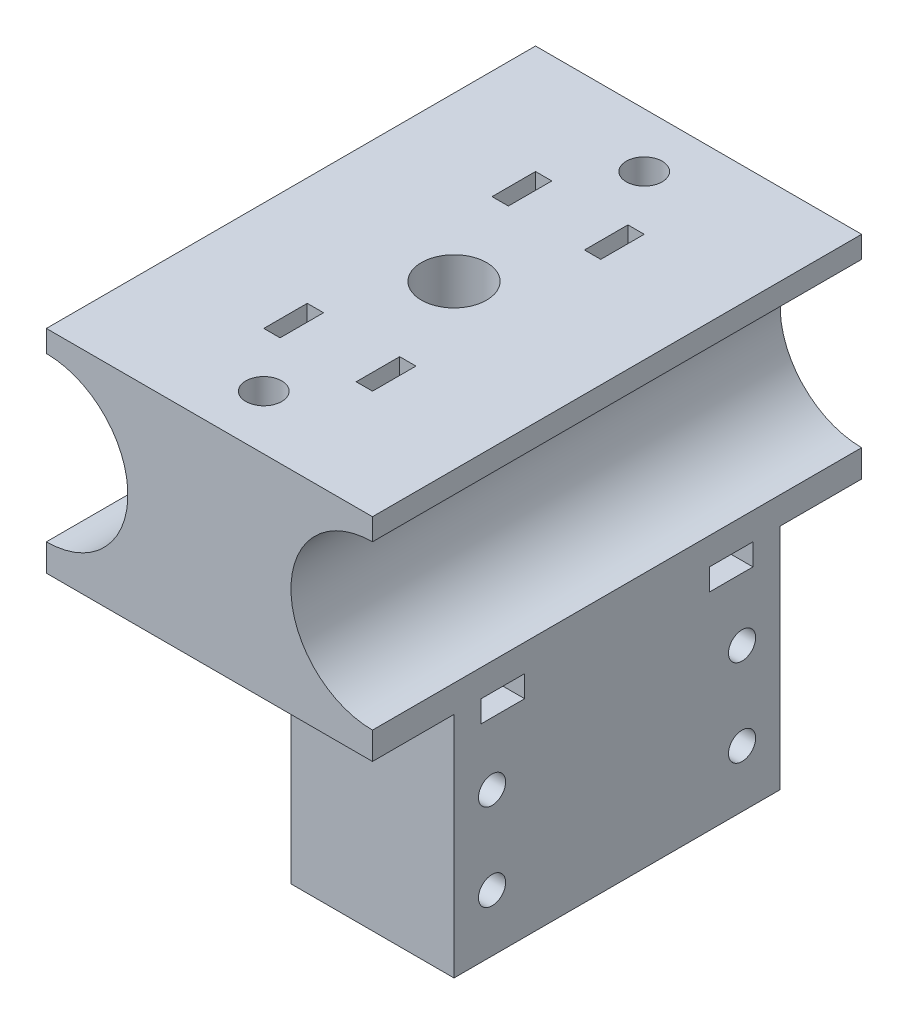
SolidWorks part; units mm, degrees
material "ABS"
ref_plane "Front Plane" through (0, 0, 0) normal (0, 0, 1) x (1, 0, 0)
ref_plane "Top Plane" through (0, 0, 0) normal (0, 1, 0) x (1, 0, 0)
ref_plane "Right Plane" through (0, 0, 0) normal (1, 0, 0) x (0, 0, -1)
sketch "Sketch1" plane through (0, 0, 0) normal (0, 0, 1) x (1, 0, 0)
  line L0 (15, 0) -> (-15, 0) construction
  line L5 (-15, 7.5) -> (-15, 9.5)
  line L6 (-15, 9.5) -> (15, 9.5)
  line L7 (15, 7.5) -> (15, 9.5)
  line L9 (-15, -7.5) -> (-15, -10)
  line L10 (-15, -10) -> (15, -10)
  line L11 (15, -7.5) -> (15, -10)
  arc A0 (15, 7.5) -> (15, -7.5) centre (15, 0) ccw
  arc A1 (-15, -7.5) -> (-15, 7.5) centre (-15, 0) ccw
  point P8 (0, 0)
  dimension "D2" = 15
  dimension "D1" = 30
  dimension "D3" = 2.5
  dimension "D4" = 2
extrude "Boss-Extrude1" add sketch "Sketch1" along normal mid plane 45
sketch "Sketch3" plane through (0, 0, 0) normal (0, 0, 1) x (1, 0, 0)
  line L0 (0, 9.5) -> (0, -10)
  line L1 (0, -10) -> (8, -10)
  line L2 (8, -10) -> (8, -3.25)
  line L3 (8, -3.25) -> (6, -3.25)
  line L4 (6, -3.25) -> (6, 2.75)
  line L5 (6, 2.75) -> (8, 2.75)
  line L6 (8, 2.75) -> (8, 9.5)
  line L7 (8, 9.5) -> (0, 9.5)
  line L8 (15, 9.5) -> (-15, 9.5) construction
  line L9 (-15, -10) -> (15, -10) construction
  dimension "D1" = 6
  dimension "D2" = 8
  dimension "D3" = 6
revolve "Cut-Revolve1" [suppressed] cut sketch "Sketch3" angle 360 about L0
hole_wizard "M4x0.7 Tapped Hole2" positions "Sketch5" profile "Sketch4" tap size "M4x0.7" standard "ANSI Metric" end condition through all
sketch "Sketch5" plane through (0, -10, 0) normal (0, -1, 0) x (-1, 0, 0)
  line L0 (0, 17.5) -> (0, -17.5) construction
  line L2 (15, -22.5) -> (-15, -22.5) construction
  point P0 (0, -17.5)
  point P2 (0, 17.5)
  dimension "D1" = 5
sketch "Sketch4" plane through (0, -10, 17.5) normal (1, 0, 0) x (0, 0, -1)
  line L0 (0, 0) -> (0, 19.5)
  line L1 (0, 19.5) -> (1.65, 19.5)
  line L2 (1.65, 19.5) -> (1.65, 0)
  line L5 (1.65, 0) -> (0, 0)
  line L11 (0, -6.35) -> (0, 107.95) construction
  dimension "Thru Tap Drill Dia." = 3.3
  dimension "Thru Tap Drill Depth" = 19.5
cosmetic thread "Hole Thread1" parameters "D2"=4
cosmetic thread "Hole Thread2" parameters "D2"=4
sketch "Sketch12" plane through (0, 0, 0) normal (0, 0, 1) x (1, 0, 0)
  line L0 (0, 0) -> (0, -31) construction
  line L1 (8, -31) -> (8, -24.5)
  line L2 (8, -24.5) -> (6, -24.5)
  line L3 (6, -24.5) -> (6, -19)
  line L4 (6, -19) -> (8, -19)
  line L5 (8, -19) -> (8, -10)
  line L9 (8, -10) -> (15, -10)
  line L10 (15, -10) -> (15, -31)
  line L11 (15, -31) -> (8, -31)
  dimension "D1" = 5.5
  dimension "D2" = 8
  dimension "D3" = 6.5
  dimension "D4" = 6
  dimension "D5" = 9
revolve "Revolve1" add sketch "Sketch12" angle 180 mid plane about L0
sketch "Sketch15" plane through (0, -31, 0) normal (0, -1, 0) x (1, 0, 0)
  line L7 (0, 15) -> (15, 15)
  line L8 (15, 22.5) -> (15, 0) construction
  line L9 (0, -8) -> (0, -15)
  line L10 (0, 15) -> (0, 8)
  line L13 (15, 15) -> (15, -15)
  line L14 (15, 0) -> (15, -22.5) construction
  line L15 (15, -15) -> (0, -15)
  arc A5 (0, -8) -> (0, 8) centre (0, 0) ccw
  arc A6 (0, -15) -> (0, 15) centre (0, 0) ccw
  arc A8 (0, -15) -> (0, 15) centre (0, 0) ccw
  arc M7 (0, -15) -> (0, 15) centre (0, 0) ccw
  dimension "D1" = 0
extrude "Boss-Extrude4" add sketch "Sketch15" against normal up to next contours L13 L7 M7 | L15 L13 M7
hole_wizard "M3x0.5 Tapped Hole1" positions "Sketch13" profile "Sketch14" tap size "M3x0.5" standard "ANSI Metric" end condition through all
sketch "Sketch13" plane through (0, 0, 0) normal (-1, 0, 0) x (0, 0, 1)
  line L0 (0, 0) -> (0, -31) construction
  line L3 (0, -21.75) -> (-11.5, -21.75) construction
  line L6 (-11.5, -17.75) -> (-11.5, -25.75) construction
  line L8 (-6, -19) -> (-6, -24.5) construction
  line L9 (-8, -31) -> (8, -31) construction
  point P0 (-11.5, -17.75)
  point P2 (-11.5, -25.75)
  point P4 (11.5, -25.75)
  point P6 (11.5, -17.75)
  point P27 (-6, -21.75)
  dimension "D1" = 8
  dimension "D2" = 11.5
sketch "Sketch14" plane through (0, -17.75, -11.5) normal (0, 1, 0) x (0, 0, 1)
  line L0 (0, 0) -> (0, 15)
  line L1 (0, 15) -> (1.25, 15)
  line L2 (1.25, 15) -> (1.25, 0)
  line L5 (1.25, 0) -> (0, 0)
  line L11 (0, -6.35) -> (0, 107.95) construction
  dimension "Thread Major Dia." = 2.5
  dimension "Thru Tap Drill Depth" = 15
sketch "Sketch7" plane through (0, 0, 0) normal (0, 0, 1) x (1, 0, 0)
  line L0 (-15, -7.5) -> (-24, -7.5)
  line L1 (-24, -7.5) -> (-24, -42.5)
  line L5 (1.1036, -10) -> (-15, -10)
  line L6 (-15, -10) -> (-15, -7.5)
  line L7 (-24, -42.5) -> (-9, -42.5)
  line L8 (-9, -42.5) -> (-9, -27.5)
  line L9 (-9, -27.5) -> (1.1036, -10)
  dimension "D1" = 9
  dimension "D2" = 35
  dimension "D3" = 15
  dimension "D4" = 60
  dimension "D6" = 15
extrude "Boss-Extrude3" [suppressed] add sketch "Sketch7" against normal mid plane 32
hole_wizard "M4x0.7 Tapped Hole1" [suppressed] positions "Sketch9" profile "Sketch8" tap size "M4x0.7" standard "ANSI Metric"
sketch "Sketch9" [suppressed] plane through (-24, 0, 0) normal (1, 0, 0) x (0, 0, -1)
  line L0 (16, -42.5) -> (-16, -42.5) construction
  point P0 (0, -37.5)
  point P2 (0, -22.5)
  dimension "D1" = 15
  dimension "D2" = 5
sketch "Sketch8" plane through (-24, -37.5, 0) normal (0, 1, 0) x (0, 0, 1)
  line L0 (0, 0) -> (0, 10.9914)
  line L1 (0, 10.9914) -> (1.65, 10)
  line L2 (1.65, 10) -> (1.65, 0)
  line L5 (1.65, 0) -> (0, 0)
  line L10 (0, 10.9914) -> (-1.65, 10) construction
  line L11 (0, -6.35) -> (0, 107.95) construction
  dimension "Tap Drill Dia." = 3.3
  dimension "Tap Drill Depth" = 10
  dimension "Drill Angle" = 118
cosmetic thread "Hole Thread5" parameters "D1"=8, "D2"=4
cosmetic thread "Hole Thread6" parameters "D1"=8, "D2"=4
sketch "Sketch2" plane through (0, 9.5, 0) normal (0, 1, 0) x (1, 0, 0)
  circle A0 centre (0, 0) radius 3
  dimension "D1" = 6
extrude "Cut-Extrude1" cut sketch "Sketch2" against normal blind 50
sketch "Sketch11" plane through (0, 0, -22.5) normal (0, 0, -1) x (-1, 0, 0)
  line L0 (-5, 9.5) -> (-5, 0)
  line L1 (-15, 9.5) -> (15, 9.5) construction
  line L2 (-15, -10) -> (-15, -12)
  line L3 (-15, -10) -> (-3.5, -10) construction
  line L4 (15, -10) -> (-15, -10) construction
  line L5 (-3.5, -10) -> (-3.5, 9.5)
  line L6 (-3.5, 9.5) -> (-5, 9.5)
  line L7 (0, 9.5) -> (0, -10) construction
  line L8 (3.5, 9.5) -> (5, 9.5)
  line L9 (3.5, -10) -> (3.5, 9.5)
  line L10 (15, -10) -> (3.5, -10) construction
  line L11 (5, 9.5) -> (5, 0)
  line L12 (-15, -10) -> (-15, -31) construction
  line L13 (-15, -12) -> (-3.5, -12)
  line L14 (-3.5, -12) -> (-3.5, -10)
  line L15 (3.5, -10) -> (3.5, -12)
  line L16 (3.5, -12) -> (15, -12)
  line L17 (15, -12) -> (15, -10)
  arc A0 (-5, 0) -> (-15, -10) centre (-15, 0) cw
  arc A1 (5, 0) -> (15, -10) centre (15, 0) ccw
  arc A3 (-15, -7.5) -> (-15, 7.5) centre (-15, 0) ccw construction
  dimension "D1" = 2
  dimension "D2" = 1.5
extrude "Cut-Extrude3" cut sketch "Sketch11" against normal blind 4 from offset 10 contours L14 L5 L6 L0 A0 L2 L13 | L15 L16 L17 A1 L11 L8 L9 offset against normal yes
mirror "Mirror1" about plane through (0, 0, 0) normal (0, 0, 1) of "Cut-Extrude3"
sketch "Sketch16" plane through (15, 0, 0) normal (1, 0, 0) x (0, 0, -1)
  line L1 (-12.5, -12) -> (-15, -12)
  line L2 (-12.5, -12) -> (-12.5, -10)
  line L3 (-12.5, -10) -> (-15, -10)
  line L4 (-15, -12) -> (-15, -10)
  line L5 (15, -10) -> (12.5, -10)
  line L6 (15, -10) -> (15, -12)
  line L7 (15, -12) -> (12.5, -12)
  line L8 (12.5, -10) -> (12.5, -12)
extrude "Cut-Extrude4" [suppressed] cut sketch "Sketch16" against normal through all
